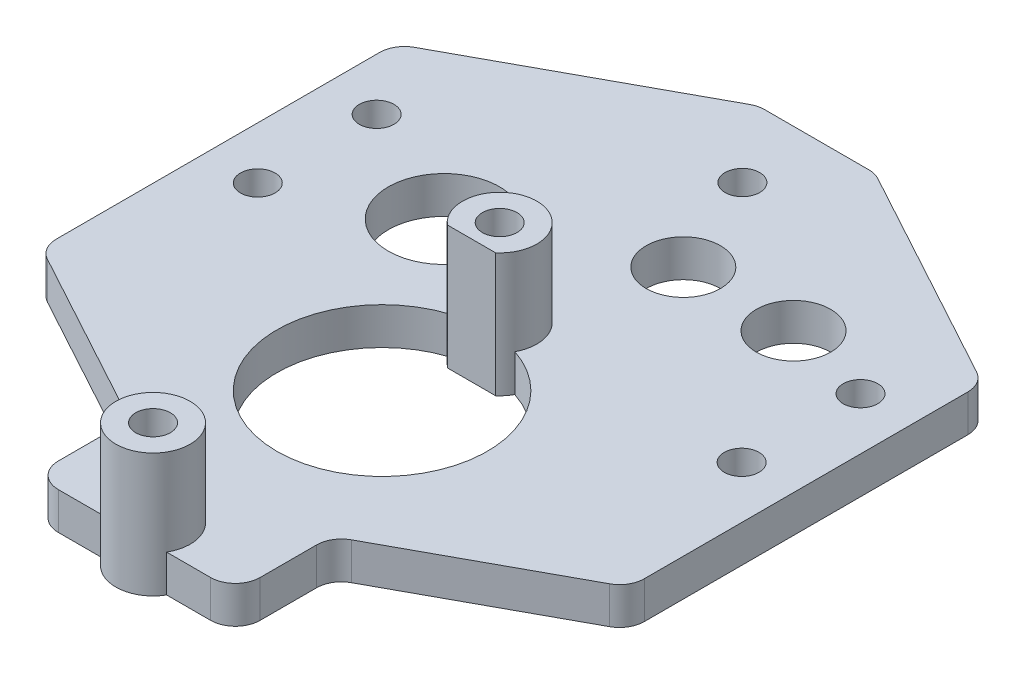
SolidWorks part; units mm, degrees
material "ПК/АБС"
ref_plane "Спереди" through (0, 0, 0) normal (0, 0, 1) x (1, 0, 0)
ref_plane "Сверху" through (0, 0, 0) normal (0, 1, 0) x (1, 0, 0)
ref_plane "Справа" through (0, 0, 0) normal (1, 0, 0) x (0, 0, -1)
sketch "Эскиз1" plane through (0, 0, 0) normal (0, 1, 0) x (1, 0, 0)
  line L1 (8.15, -20) -> (8.15, -12.25)
  line L2 (8.15, -12.25) -> (23.75, -3.7573)
  line L3 (23.75, -3.7573) -> (23.75, 24.7427)
  line L4 (23.75, 24.7427) -> (4.725, 35.1)
  line L5 (4.725, 35.1) -> (-4.725, 35.1)
  line L6 (-4.725, 35.1) -> (-23.75, 24.7427)
  line L7 (-23.75, 24.7427) -> (-23.75, -3.7573)
  line L8 (-23.75, -3.7573) -> (-8.15, -12.25)
  line L9 (-8.15, -12.25) -> (-8.15, -20)
  line L11 (0, 45.6052) -> (0, -40.3782) construction
  line L12 (-36.7129, 0) -> (34.77, 0) construction
  line L13 (-8.15, -20) -> (8.15, -20)
  circle A0 centre (0, 0) radius 8.5
  circle A1 centre (-9.5, 14.5) radius 4.5
  circle A2 centre (3.53, 20.8) radius 3
  circle A3 centre (12.43, 20.8) radius 3
  circle A5 centre (19.54, 19.1) radius 1.4
  circle A6 centre (19.54, 9.5) radius 1.4
  circle A7 centre (-19.54, 19.1) radius 1.4
  circle A8 centre (-19.54, 9.5) radius 1.4
  circle A9 centre (0, 29.1) radius 1.4
  point P0 (0, -20)
  point P18 (0, 35.1)
  dimension "D3" = 17
  dimension "D10" = 9
  dimension "D14" = 6
  dimension "D16" = 6
  dimension "D19" = 2.8
  dimension "D20" = 2.8
  dimension "D23" = 2.8
  dimension "D1" = 55.1
  dimension "D2" = 47.5
  dimension "D4" = 7.75
  dimension "D5" = 28.5
  dimension "D6" = 9.45
  dimension "D7" = 16.3
  dimension "D8" = 9.5
  dimension "D9" = 14.5
  dimension "D11" = 20
  dimension "D12" = 20.8
  dimension "D13" = 3.53
  dimension "D15" = 8.9
  dimension "D17" = 7.11
  dimension "D18" = 1.7
  dimension "D21" = 9.6
  dimension "D22" = 29.1
extrude "Бобышка-Вытянуть1" add sketch "Эскиз1" along normal blind 3
fillet "Скругление1" radius 2 10 edges at (4.725, 1.5, -35.1) (-4.725, 1.5, -35.1) (23.75, 1.5, -24.7427) (-23.75, 1.5, -24.7427) (-23.75, 1.5, 3.7573) (23.75, 1.5, 3.7573) (8.15, 1.5, 20) (-8.15, 1.5, 20) (-8.15, 1.5, 12.25) (8.15, 1.5, 12.25)
sketch "Эскиз2" plane through (0, 3, 0) normal (0, 1, 0) x (1, 0, 0)
  line L0 (-1.9498, 7.22) -> (1.9498, 7.22)
  circle A0 centre (0, -18.5) radius 3
  arc A1 (1.9498, 7.22) -> (-1.9498, 7.22) centre (0, 9.5) ccw
  dimension "D2" = 6
  dimension "D4" = 6
  dimension "D1" = 18.5
  dimension "D3" = 9.5
  dimension "D5" = 2.28
extrude "Бобышка-Вытянуть2" add sketch "Эскиз2" along normal blind 7 and the other way blind 3
sketch "Эскиз3" plane through (0, 10, 0) normal (0, 1, 0) x (1, 0, 0)
  circle A0 centre (0, 9.5) radius 1.4
  circle A1 centre (0, -18.5) radius 1.4
  dimension "D1" = 2.8
  dimension "D2" = 2.8
extrude "Вырез-Вытянуть1" cut sketch "Эскиз3" against normal through all both and the other way through all
